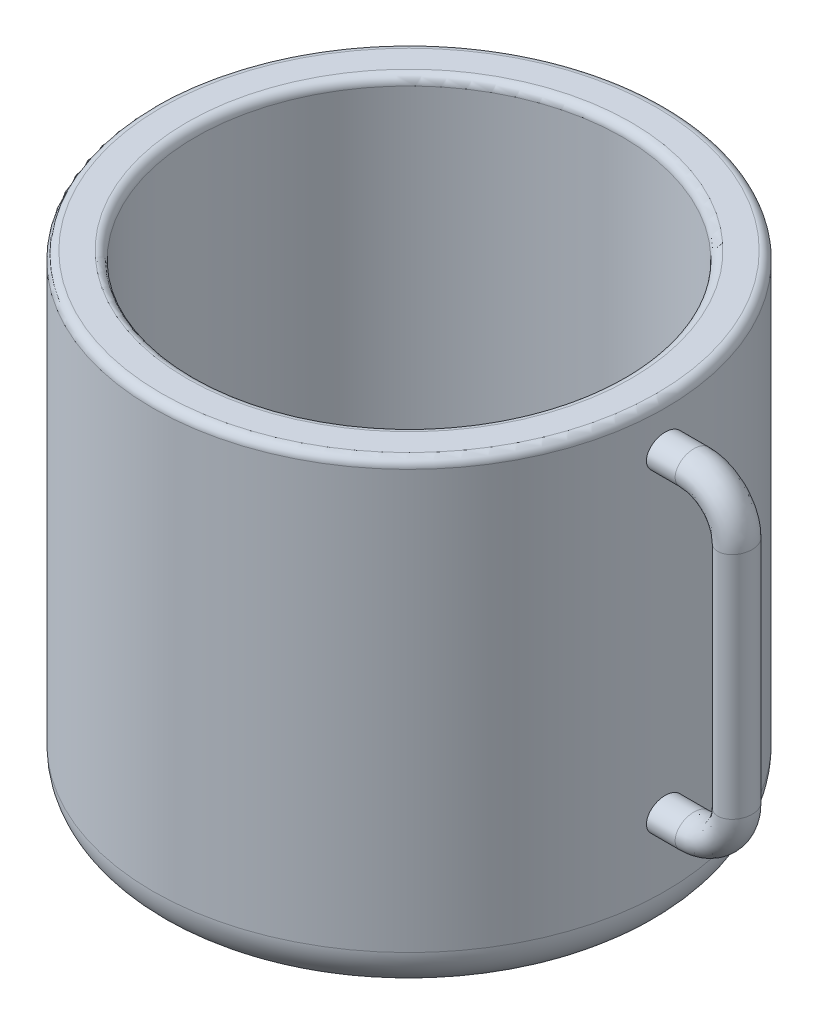
SolidWorks part; units mm, degrees
ref_plane "Front Plane" through (0, 0, 0) normal (0, 0, 1) x (1, 0, 0)
ref_plane "Top Plane" through (0, 0, 0) normal (0, 1, 0) x (1, 0, 0)
ref_plane "Right Plane" through (0, 0, 0) normal (1, 0, 0) x (0, 0, -1)
sketch "Sketch6" plane through (0, 0, 0) normal (0, 0, 1) x (1, 0, 0)
  line L0 (0, 0) -> (0, 35.4426)
  line L1 (-2, 37.4426) -> (-8, 37.4426)
  line L2 (-10, 35.4426) -> (-10, -62.5574)
  line L3 (-10, -62.5574) -> (-60, -62.5574)
  line L4 (-60, -62.5574) -> (-60, -72.5574)
  line L5 (-60, -72.5574) -> (-10, -72.5574)
  line L6 (0, -62.5574) -> (0, 0)
  line L7 (-60, 37.4426) -> (-60, -62.5574) construction
  arc A0 (-10, -72.5574) -> (0, -62.5574) centre (-10, -62.5574) ccw
  arc A1 (-8, 37.4426) -> (-10, 35.4426) centre (-8, 35.4426) ccw
  arc A2 (0, 35.4426) -> (-2, 37.4426) centre (-2, 35.4426) ccw
  dimension "D1" = 10
  dimension "D2" = 2
revolve "Revolve7" add sketch "Sketch6" angle 360 about L7
sketch "Sketch8" plane through (0, 0, 0) normal (1, 0, 0) x (0, 0, -1)
  ellipse E0 centre (0, 26.9469) end of major axis (4.3974, 26.9469) minor radius 3.6392
sketch "Sketch10" plane through (0, 0, 0) normal (0, 0, 1) x (1, 0, 0)
  line L0 (0, 26.9469) -> (6.7264, 26.9469)
  line L1 (0, 23.3077) -> (0, 30.5861) construction
  line L2 (16.7264, 16.9469) -> (16.7264, -36.7468)
  line L3 (6.7264, -46.7468) -> (0, -46.7468)
  arc A0 (16.7264, -36.7468) -> (6.7264, -46.7468) centre (6.7264, -36.7468) cw
  arc A1 (6.7264, 26.9469) -> (16.7264, 16.9469) centre (6.7264, 16.9469) cw
  dimension "D1" = 10
sweep "Sweep4" add profiles "Sketch8" path "Sketch10"
